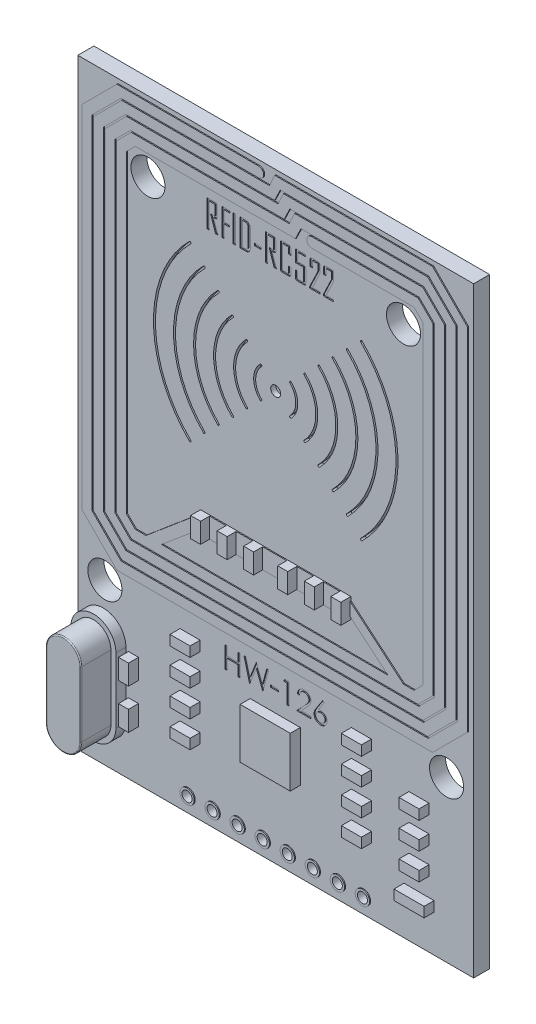
SolidWorks part; units mm, degrees
ref_plane "Alzado" through (0, 0, 0) normal (0, 0, 1) x (1, 0, 0)
ref_plane "Planta" through (0, 0, 0) normal (0, 1, 0) x (1, 0, 0)
ref_plane "Vista lateral" through (0, 0, 0) normal (1, 0, 0) x (0, 0, -1)
sketch "Croquis1" plane through (0, 0, 0) normal (0, 0, 1) x (1, 0, 0)
  line L0 (0, 0) -> (0, 18.9964) construction
  line L1 (-19.75, 30) -> (19.75, 30)
  line L2 (-19.75, 30) -> (-19.75, -30)
  line L3 (-19.75, -30) -> (19.75, -30)
  line L4 (19.75, 30) -> (19.75, -30)
  line L5 (-19.75, 30) -> (19.75, -30) construction
  line L6 (-19.75, -30) -> (19.75, 30) construction
  circle A0 centre (-12.75, 23) radius 1.7
  circle A1 centre (12.75, 23) radius 1.7
  circle A2 centre (-17.05, -14) radius 1.7
  circle A3 centre (17.05, -14) radius 1.7
  point P0 (0, 0)
  dimension "D3" = 3.4
  dimension "D6" = 3.4
  dimension "D1" = 60
  dimension "D2" = 39.5
  dimension "D4" = 7
  dimension "D5" = 7
  dimension "D7" = 2.7
  dimension "D8" = 16
extrude "Saliente-Extruir1" add sketch "Croquis1" along normal blind 1.6
sketch "Croquis2" plane through (0, 0, 1.6) normal (0, 0, 1) x (1, 0, 0)
  line L0 (-17.2, -25.25) -> (-17.2, -18.75) construction
  line L1 (-19.45, -25.25) -> (-19.45, -18.75)
  line L2 (-14.95, -25.25) -> (-14.95, -18.75)
  line L3 (-19.75, 30) -> (-19.75, -30) construction
  line L4 (-19.75, -30) -> (19.75, -30) construction
  arc A0 (-19.45, -25.25) -> (-14.95, -25.25) centre (-17.2, -25.25) ccw
  arc A1 (-14.95, -18.75) -> (-19.45, -18.75) centre (-17.2, -18.75) ccw
  point P2 (-17.2, -22)
  point P9 (-17.2, -27.5)
  dimension "D1" = 2.25
  dimension "D2" = 6.5
  dimension "D3" = 0.3
  dimension "D4" = 2.5
extrude "Saliente-Extruir2" add sketch "Croquis2" along normal blind 1
sketch "Croquis3" plane through (0, 0, 2.6) normal (0, 0, 1) x (1, 0, 0)
  line L0 (-18.95, -18.75) -> (-18.95, -25.25)
  line L1 (-15.45, -25.25) -> (-15.45, -18.75)
  line L2 (-14.95, -25.25) -> (-14.95, -18.75)
  line L3 (-19.45, -18.75) -> (-19.45, -25.25)
  line L4 (-14.95, -25.25) -> (-14.95, -18.75)
  line L5 (-19.45, -18.75) -> (-19.45, -25.25)
  arc A0 (-15.45, -18.75) -> (-18.95, -18.75) centre (-17.2, -18.75) ccw
  arc A1 (-18.95, -25.25) -> (-15.45, -25.25) centre (-17.2, -25.25) ccw
  arc A2 (-19.45, -25.25) -> (-14.95, -25.25) centre (-17.2, -25.25) ccw
  arc A3 (-14.95, -18.75) -> (-19.45, -18.75) centre (-17.2, -18.75) ccw
  arc A4 (-19.45, -25.25) -> (-14.95, -25.25) centre (-17.2, -25.25) ccw
  arc A5 (-14.95, -18.75) -> (-19.45, -18.75) centre (-17.2, -18.75) ccw
  dimension "D1" = 0
  dimension "D2" = 0.5
extrude "Saliente-Extruir3" add sketch "Croquis3" along normal blind 3 contours A0 L0 A1 L1
fillet "Redondeo1" radius 0.1 4 edges at (-17.2, -17, 5.6) (-15.45, -22, 5.6) (-17.2, -27, 5.6) (-18.95, -22, 5.6)
sketch "Croquis4" plane through (0, 0, 1.6) normal (0, 0, 1) x (1, 0, 0)
  line L0 (-19.75, -30) -> (19.75, -30) construction
  line L1 (0, -9.1522) -> (0, -4.1522) construction
  line L2 (-19.25, 26.0478) -> (-15.75, 29.5478)
  line L3 (-18.25, 25.6336) -> (-15.3358, 28.5478)
  line L4 (-19.25, -8.9522) -> (-15.75, -12.4522)
  line L5 (-15.75, 29.5478) -> (-1.601, 29.5478)
  line L6 (-19.25, 26.0478) -> (-19.25, -8.9522)
  line L7 (-15.75, -12.4522) -> (15.75, -12.4522)
  line L8 (19.25, 26.0478) -> (19.25, -8.9522)
  line L9 (15.75, -12.4522) -> (19.25, -8.9522)
  line L10 (15.75, 29.5478) -> (19.25, 26.0478)
  line L11 (-15.3358, 28.5478) -> (-1.601, 28.5478)
  line L12 (15.3358, 28.5478) -> (18.25, 25.6336)
  line L13 (18.25, 25.6336) -> (18.25, -8.538)
  line L14 (15.3358, -11.4522) -> (18.25, -8.538)
  line L15 (-15.3358, -11.4522) -> (15.3358, -11.4522)
  line L16 (-18.25, -8.538) -> (-15.3358, -11.4522)
  line L17 (-18.25, 25.6336) -> (-18.25, -8.538)
  line L19 (-18.1, 25.5714) -> (-15.2737, 28.3978)
  line L20 (-15.2737, 28.3978) -> (-0.5349, 28.3978)
  line L21 (15.2737, 28.3978) -> (18.1, 25.5714)
  line L22 (18.1, 25.5714) -> (18.1, -8.4759)
  line L23 (15.2737, -11.3022) -> (18.1, -8.4759)
  line L24 (-15.2737, -11.3022) -> (15.2737, -11.3022)
  line L25 (-18.1, -8.4759) -> (-15.2737, -11.3022)
  line L26 (-18.1, 25.5714) -> (-18.1, -8.4759)
  line L27 (-17.1, 25.1572) -> (-14.8594, 27.3978)
  line L28 (-14.8594, 27.3978) -> (0, 27.3978)
  line L29 (14.8594, 27.3978) -> (17.1, 25.1572)
  line L30 (17.1, 25.1572) -> (17.1, -8.0617)
  line L31 (14.8594, -10.3022) -> (17.1, -8.0617)
  line L32 (-14.8594, -10.3022) -> (14.8594, -10.3022)
  line L33 (-17.1, -8.0617) -> (-14.8594, -10.3022)
  line L34 (-17.1, 25.1572) -> (-17.1, -8.0617)
  line L36 (-16.95, 25.0951) -> (-14.7973, 27.2478)
  line L37 (-14.7973, 27.2478) -> (0.3296, 27.2478)
  line L38 (14.7973, 27.2478) -> (16.95, 25.0951)
  line L39 (16.95, 25.0951) -> (16.95, -7.9995)
  line L40 (14.7973, -10.1522) -> (16.95, -7.9995)
  line L41 (-14.7973, -10.1522) -> (14.7973, -10.1522)
  line L42 (-16.95, -7.9995) -> (-14.7973, -10.1522)
  line L43 (-16.95, 25.0951) -> (-16.95, -7.9995)
  line L44 (-15.95, 24.6809) -> (-14.3831, 26.2478)
  line L45 (-14.3831, 26.2478) -> (0.9585, 26.2478)
  line L46 (14.3831, 26.2478) -> (15.95, 24.6809)
  line L47 (15.95, 24.6809) -> (15.95, -7.5853)
  line L48 (14.3831, -9.1522) -> (15.95, -7.5853)
  line L49 (-14.3831, -9.1522) -> (14.3831, -9.1522)
  line L50 (-15.95, -7.5853) -> (-14.3831, -9.1522)
  line L51 (-15.95, 24.6809) -> (-15.95, -7.5853)
  line L53 (-15.8, 24.6187) -> (-14.321, 26.0978)
  line L54 (-14.321, 26.0978) -> (1.4391, 26.0978)
  line L55 (14.321, 26.0978) -> (15.8, 24.6187)
  line L56 (15.8, 24.6187) -> (15.8, -7.5232)
  line L57 (14.321, -9.0022) -> (15.8, -7.5232)
  line L58 (-14.321, -9.0022) -> (14.321, -9.0022)
  line L59 (-15.8, -7.5232) -> (-14.321, -9.0022)
  line L60 (-15.8, 24.6187) -> (-15.8, -7.5232)
  line L61 (-14.8, 24.2045) -> (-13.9067, 25.0978)
  line L62 (-13.9067, 25.0978) -> (2.0668, 25.0978)
  line L63 (13.9067, 25.0978) -> (14.8, 24.2045)
  line L64 (14.8, 24.2045) -> (14.8, -7.109)
  line L65 (13.9067, -8.0022) -> (14.8, -7.109)
  line L66 (-13.9067, -8.0022) -> (-12.8445, -8.0022)
  line L67 (-14.8, -7.109) -> (-13.9067, -8.0022)
  line L68 (-14.8, 24.2045) -> (-14.8, -7.109)
  line L69 (0.3296, 27.2478) -> (0.8823, 28.3978)
  line L70 (0, 27.3978) -> (0.5526, 28.5478)
  line L71 (0, 29.5478) -> (-0.5349, 28.3978)
  line L72 (0.5526, 28.5478) -> (15.3358, 28.5478)
  line L73 (-15.3358, 28.5478) -> (15.3358, 28.5478) construction
  line L74 (0.8823, 28.3978) -> (15.2737, 28.3978)
  line L75 (-15.2737, 28.3978) -> (15.2737, 28.3978) construction
  line L76 (1.4391, 26.0978) -> (1.9943, 27.2478)
  line L77 (0, 29.5478) -> (15.75, 29.5478)
  line L78 (-15.75, 29.5478) -> (15.75, 29.5478) construction
  line L79 (0.9585, 26.2478) -> (1.5112, 27.3978)
  line L81 (1.9943, 27.2478) -> (14.7973, 27.2478)
  line L82 (-14.7973, 27.2478) -> (14.7973, 27.2478) construction
  line L83 (1.5112, 27.3978) -> (14.8594, 27.3978)
  line L84 (-14.8594, 27.3978) -> (14.8594, 27.3978) construction
  line L85 (2.6219, 26.2478) -> (2.0668, 25.0978)
  line L86 (3.6973, 26.0978) -> (14.321, 26.0978)
  line L87 (-14.321, 26.0978) -> (14.321, 26.0978) construction
  line L88 (2.6219, 26.2478) -> (14.3831, 26.2478)
  line L89 (-14.3831, 26.2478) -> (14.3831, 26.2478) construction
  line L90 (3.6973, 25.0978) -> (13.9067, 25.0978)
  line L91 (-13.9067, 25.0978) -> (13.9067, 25.0978) construction
  line L97 (-7.5, -4.8061) -> (-7.5, -5.1522)
  line L98 (-7.5, -3.1522) -> (7.5, -3.1522)
  line L99 (-7.5, -3.1522) -> (-7.5, -3.4984)
  line L100 (-7.5, -5.1522) -> (7.5, -5.1522)
  line L101 (7.5, -3.1522) -> (7.5, -3.4984)
  line L102 (-7.5, -3.1522) -> (7.5, -5.1522) construction
  line L103 (-7.5, -5.1522) -> (7.5, -3.1522) construction
  line L108 (-7.8222, -3.7699) -> (-12.3908, -7.6199)
  line L109 (-7.5, -4.8061) -> (-11.2927, -8.0022)
  line L112 (19.25, -29.5) -> (19.25, 29.5)
  line L113 (19.25, 29.5) -> (-19.25, 29.5)
  line L114 (-19.25, 29.5) -> (-19.25, -29.5)
  line L115 (-19.25, -29.5) -> (19.25, -29.5)
  line L119 (-19.25, -29.5) -> (19.25, -29.5)
  line L120 (-12.3908, -7.6199) -> (-12.8445, -8.0022)
  line L121 (-7.8222, -3.7699) -> (-7.5, -3.4984)
  line L122 (-11.2927, -8.0022) -> (11.2927, -8.0022)
  line L123 (-13.9067, -8.0022) -> (13.9067, -8.0022) construction
  line L124 (7.5, -4.8061) -> (11.2927, -8.0022)
  line L125 (7.8222, -3.7699) -> (7.5, -3.4984)
  line L126 (12.3908, -7.6199) -> (12.8445, -8.0022)
  line L127 (7.8222, -3.7699) -> (12.3908, -7.6199)
  line L128 (7.5, -4.8061) -> (7.5, -5.1522)
  line L129 (12.8445, -8.0022) -> (13.9067, -8.0022)
  arc A0 (-1.601, 28.5478) -> (-1.601, 29.5478) centre (-1.601, 29.0478) ccw
  arc A1 (3.6973, 26.0978) -> (3.6973, 25.0978) centre (3.6973, 25.5978) ccw
  point P6 (-19.25, 29.5478)
  point P7 (19.25, -12.4522)
  point P9 (-19.25, -12.4522)
  point P10 (19.25, 29.5478)
  dimension "D2" = 1
  dimension "D3" = 42
  dimension "D4" = 38.5
  dimension "D7" = 1
  dimension "D11" = 1
  dimension "D5" = 5
  dimension "D6" = 15
  dimension "D12" = 17.5478
  dimension "D13" = 2
  dimension "D14" = 0.5
extrude "Saliente-Extruir4" add sketch "Croquis4" along normal blind 0.1 contours L86 A1 L90 L63 L64 L65 L129 L126 L127 L125 L101 L98 L99 L121 L108 L120 L66 L67 L68 L61 L62 L85 L88 L46 L47 L48 L49 L50 L51 L44 L45 L79 L83 L29 L30 L31 L32 L33 L34 L27 L28 L70 L72 L12 L13 L14 L15 L16 L17 L3 L11
sketch "Croquis5" plane through (0, 0, 1.6) normal (0, 0, 1) x (1, 0, 0)
  line L1 (0, -3.1522) -> (0, 6.8478) construction
  line L2 (-7.5, -3.1522) -> (7.5, -3.1522) construction
  line L3 (-0.5, 10.8478) -> (-9.5579, 10.8478) construction
  circle A1 centre (0, 10.8478) radius 0.5
  arc A2 (-1.4142, 12.262) -> (-1.4142, 9.4336) centre (0, 10.8478) ccw
  arc A3 (-1.5556, 12.4034) -> (-1.5556, 9.2921) centre (0, 10.8478) ccw
  arc A4 (-2.8284, 13.6762) -> (-2.8284, 8.0194) centre (0, 10.8478) ccw
  arc A5 (-2.9698, 13.8176) -> (-2.9698, 7.8779) centre (0, 10.8478) ccw
  arc A6 (-4.2426, 15.0904) -> (-4.2426, 6.6051) centre (0, 10.8478) ccw
  arc A7 (-4.3841, 15.2318) -> (-4.3841, 6.4637) centre (0, 10.8478) ccw
  arc A8 (-5.6569, 16.5046) -> (-5.6569, 5.1909) centre (0, 10.8478) ccw
  arc A9 (-5.7983, 16.6461) -> (-5.7983, 5.0495) centre (0, 10.8478) ccw
  arc A10 (-7.0711, 17.9188) -> (-7.0711, 3.7767) centre (0, 10.8478) ccw
  arc A11 (-7.2125, 18.0603) -> (-7.2125, 3.6353) centre (0, 10.8478) ccw
  arc A12 (-8.4853, 19.3331) -> (-8.4853, 2.3625) centre (0, 10.8478) ccw
  arc A13 (-8.6267, 19.4745) -> (-8.6267, 2.2211) centre (0, 10.8478) ccw
  circle A14 centre (0, 10.8478) radius 12.2 construction
  circle A15 centre (0, 10.8478) radius 12 construction
  circle A16 centre (0, 10.8478) radius 10.2 construction
  circle A17 centre (0, 10.8478) radius 10 construction
  circle A18 centre (0, 10.8478) radius 8.2 construction
  circle A19 centre (0, 10.8478) radius 8 construction
  circle A20 centre (0, 10.8478) radius 6.2 construction
  circle A21 centre (0, 10.8478) radius 6 construction
  circle A22 centre (0, 10.8478) radius 4.2 construction
  circle A23 centre (0, 10.8478) radius 4 construction
  circle A24 centre (0, 10.8478) radius 2.2 construction
  circle A25 centre (0, 10.8478) radius 2 construction
  arc A26 (-8.4853, 2.3625) -> (-8.6267, 2.2211) centre (-8.556, 2.2918) cw
  arc A27 (-7.2125, 3.6353) -> (-7.0711, 3.7767) centre (-7.1418, 3.706) ccw
  arc A28 (-5.7983, 5.0495) -> (-5.6569, 5.1909) centre (-5.7276, 5.1202) ccw
  arc A29 (-4.3841, 6.4637) -> (-4.2426, 6.6051) centre (-4.3134, 6.5344) ccw
  arc A30 (-2.9698, 7.8779) -> (-2.8284, 8.0194) centre (-2.8991, 7.9486) ccw
  arc A31 (-1.5556, 9.2921) -> (-1.4142, 9.4336) centre (-1.4849, 9.3629) ccw
  arc A32 (-8.6267, 19.4745) -> (-8.4853, 19.3331) centre (-8.556, 19.4038) cw
  arc A33 (-7.0711, 17.9188) -> (-7.2125, 18.0603) centre (-7.1418, 17.9896) ccw
  arc A34 (-5.6569, 16.5046) -> (-5.7983, 16.6461) centre (-5.7276, 16.5753) ccw
  arc A35 (-1.4142, 12.262) -> (-1.5556, 12.4034) centre (-1.4849, 12.3327) ccw
  arc A36 (-4.2426, 15.0904) -> (-4.3841, 15.2318) centre (-4.3134, 15.1611) ccw
  arc A37 (-2.8284, 13.6762) -> (-2.9698, 13.8176) centre (-2.8991, 13.7469) ccw
  arc A38 (2.8284, 13.6762) -> (2.9698, 13.8176) centre (2.8991, 13.7469) cw
  arc A39 (4.2426, 15.0904) -> (4.3841, 15.2318) centre (4.3134, 15.1611) cw
  arc A40 (1.4142, 12.262) -> (1.5556, 12.4034) centre (1.4849, 12.3327) cw
  arc A41 (5.6569, 16.5046) -> (5.7983, 16.6461) centre (5.7276, 16.5753) cw
  arc A42 (7.0711, 17.9188) -> (7.2125, 18.0603) centre (7.1418, 17.9896) cw
  arc A43 (8.6267, 19.4745) -> (8.4853, 19.3331) centre (8.556, 19.4038) ccw
  arc A44 (1.5556, 9.2921) -> (1.4142, 9.4336) centre (1.4849, 9.3629) cw
  arc A45 (2.9698, 7.8779) -> (2.8284, 8.0194) centre (2.8991, 7.9486) cw
  arc A46 (4.3841, 6.4637) -> (4.2426, 6.6051) centre (4.3134, 6.5344) cw
  arc A47 (5.7983, 5.0495) -> (5.6569, 5.1909) centre (5.7276, 5.1202) cw
  arc A48 (7.2125, 3.6353) -> (7.0711, 3.7767) centre (7.1418, 3.706) cw
  arc A49 (8.4853, 2.3625) -> (8.6267, 2.2211) centre (8.556, 2.2918) ccw
  arc A50 (8.6267, 19.4745) -> (8.6267, 2.2211) centre (0, 10.8478) cw
  arc A51 (8.4853, 19.3331) -> (8.4853, 2.3625) centre (0, 10.8478) cw
  arc A52 (7.2125, 18.0603) -> (7.2125, 3.6353) centre (0, 10.8478) cw
  arc A53 (7.0711, 17.9188) -> (7.0711, 3.7767) centre (0, 10.8478) cw
  arc A54 (5.7983, 16.6461) -> (5.7983, 5.0495) centre (0, 10.8478) cw
  arc A55 (5.6569, 16.5046) -> (5.6569, 5.1909) centre (0, 10.8478) cw
  arc A56 (4.3841, 15.2318) -> (4.3841, 6.4637) centre (0, 10.8478) cw
  arc A57 (4.2426, 15.0904) -> (4.2426, 6.6051) centre (0, 10.8478) cw
  arc A58 (2.9698, 13.8176) -> (2.9698, 7.8779) centre (0, 10.8478) cw
  arc A59 (2.8284, 13.6762) -> (2.8284, 8.0194) centre (0, 10.8478) cw
  arc A60 (1.5556, 12.4034) -> (1.5556, 9.2921) centre (0, 10.8478) cw
  arc A61 (1.4142, 12.262) -> (1.4142, 9.4336) centre (0, 10.8478) cw
  dimension "D1" = 0.2
  dimension "D2" = 2
  dimension "D3" = 2
  dimension "D4" = 2
  dimension "D5" = 2
  dimension "D6" = 2
extrude "Cortar-Extruir1" cut sketch "Croquis5" against normal blind 0.5
sketch "Croquis7" plane through (0, 0, 1.6) normal (0, 0, 1) x (1, 0, 0)
  line L0 (-7.5, -5.1522) -> (7.5, -5.1522) construction
  line L1 (-7.5, -3.1522) -> (-6.5, -3.1522)
  line L2 (-7.5, -3.1522) -> (-7.5, -5.1522)
  line L3 (-7.5, -5.1522) -> (-6.5, -5.1522)
  line L4 (-6.5, -3.1522) -> (-6.5, -5.1522)
  line L5 (0, -5.1522) -> (0, -7.1403) construction
  line L6 (-7.5, -5.1522) -> (7.5, -5.1522) construction
  line L7 (7.5, -5.1522) -> (6.5, -5.1522)
  line L8 (7.5, -3.1522) -> (6.5, -3.1522)
  line L9 (-4.85, -3.1522) -> (-4.85, -5.1522)
  line L10 (-4.85, -3.1522) -> (-3.85, -3.1522)
  line L11 (-3.85, -3.1522) -> (-3.85, -5.1522)
  line L12 (-4.85, -5.1522) -> (-3.85, -5.1522)
  line L13 (2.2, -5.1522) -> (1.2, -5.1522)
  line L14 (-2.2, -3.1522) -> (-2.2, -5.1522)
  line L15 (-2.2, -3.1522) -> (-1.2, -3.1522)
  line L16 (-1.2, -3.1522) -> (-1.2, -5.1522)
  line L17 (-2.2, -5.1522) -> (-1.2, -5.1522)
  line L18 (-7.5, -3.1522) -> (-6.5, -3.1522)
  line L19 (-7.5, -5.1522) -> (-6.5, -5.1522)
  line L20 (1.2, -3.1522) -> (1.2, -5.1522)
  line L21 (2.2, -3.1522) -> (1.2, -3.1522)
  line L22 (2.2, -3.1522) -> (2.2, -5.1522)
  line L23 (4.85, -5.1522) -> (3.85, -5.1522)
  line L24 (3.85, -3.1522) -> (3.85, -5.1522)
  line L25 (4.85, -3.1522) -> (3.85, -3.1522)
  line L26 (4.85, -3.1522) -> (4.85, -5.1522)
  line L27 (6.5, -3.1522) -> (6.5, -5.1522)
  line L28 (7.5, -5.1522) -> (6.5, -5.1522)
  line L29 (7.5, -3.1522) -> (7.5, -5.1522)
  line L30 (7.5, -3.1522) -> (6.5, -3.1522)
  dimension "D1" = 1
  dimension "D2" = 3
extrude "Saliente-Extruir5" add sketch "Croquis7" along normal blind 1 contours L4 L1 L2 L3 | L9 L12 L11 L10 | L14 L17 L16 L15 | L22 L21 L20 L13 | L26 L25 L24 L23 | L29 L8 L27 L7
sketch "Croquis8" plane through (0, 0, 1.6) normal (0, 0, 1) x (1, 0, 0)
  line L0 (0, -30) -> (0, -25.4316) construction
  line L1 (-2.5511, -17) -> (2.4489, -17)
  line L2 (-2.5511, -17) -> (-2.5511, -22)
  line L3 (-2.5511, -22) -> (2.4489, -22)
  line L4 (2.4489, -17) -> (2.4489, -22)
  line L5 (-2.5511, -17) -> (2.4489, -22) construction
  line L6 (-2.5511, -22) -> (2.4489, -17) construction
  line L7 (-9.5511, -14.4522) -> (-7.5511, -14.4522)
  line L8 (-9.5511, -14.4522) -> (-9.5511, -15.4522)
  line L9 (-9.5511, -15.4522) -> (-7.5511, -15.4522)
  line L10 (-7.5511, -14.4522) -> (-7.5511, -15.4522)
  line L11 (-9.5511, -14.4522) -> (-7.5511, -15.4522) construction
  line L12 (-9.5511, -15.4522) -> (-7.5511, -14.4522) construction
  line L13 (-19.75, -30) -> (19.75, -30) construction
  line L14 (19.75, 30) -> (-19.75, 30) construction
  line L15 (19.75, -30) -> (19.75, 30) construction
  line L16 (-15.75, -12.4522) -> (15.75, -12.4522) construction
  line L17 (-9.5511, -17.1122) -> (-9.5511, -18.1122)
  line L18 (-9.5511, -17.1122) -> (-7.5511, -17.1122)
  line L19 (-7.5511, -17.1122) -> (-7.5511, -18.1122)
  line L20 (-9.5511, -18.1122) -> (-7.5511, -18.1122)
  line L21 (-9.5511, -19.7722) -> (-9.5511, -20.7722)
  line L22 (-9.5511, -19.7722) -> (-7.5511, -19.7722)
  line L23 (-7.5511, -19.7722) -> (-7.5511, -20.7722)
  line L24 (-9.5511, -20.7722) -> (-7.5511, -20.7722)
  line L25 (-9.5511, -22.4322) -> (-9.5511, -23.4322)
  line L26 (-9.5511, -22.4322) -> (-7.5511, -22.4322)
  line L27 (-7.5511, -22.4322) -> (-7.5511, -23.4322)
  line L28 (-9.5511, -23.4322) -> (-7.5511, -23.4322)
  line L29 (9.5511, -15.4522) -> (7.5511, -14.4522) construction
  line L30 (9.5511, -14.4522) -> (7.5511, -15.4522) construction
  line L31 (9.5511, -23.4322) -> (7.5511, -23.4322)
  line L32 (7.5511, -22.4322) -> (7.5511, -23.4322)
  line L33 (9.5511, -22.4322) -> (7.5511, -22.4322)
  line L34 (9.5511, -22.4322) -> (9.5511, -23.4322)
  line L35 (9.5511, -20.7722) -> (7.5511, -20.7722)
  line L36 (7.5511, -19.7722) -> (7.5511, -20.7722)
  line L37 (9.5511, -19.7722) -> (7.5511, -19.7722)
  line L38 (9.5511, -19.7722) -> (9.5511, -20.7722)
  line L39 (9.5511, -18.1122) -> (7.5511, -18.1122)
  line L40 (7.5511, -17.1122) -> (7.5511, -18.1122)
  line L41 (9.5511, -17.1122) -> (7.5511, -17.1122)
  line L42 (9.5511, -17.1122) -> (9.5511, -18.1122)
  line L43 (7.5511, -14.4522) -> (7.5511, -15.4522)
  line L44 (9.5511, -15.4522) -> (7.5511, -15.4522)
  line L45 (9.5511, -14.4522) -> (9.5511, -15.4522)
  line L46 (9.5511, -14.4522) -> (7.5511, -14.4522)
  line L47 (-14.6935, -23.004) -> (-14.6935, -25.004)
  line L48 (-14.6935, -19.004) -> (-13.6935, -19.004)
  line L49 (-14.6935, -19.004) -> (-14.6935, -21.004)
  line L50 (-14.6935, -21.004) -> (-13.6935, -21.004)
  line L51 (-13.6935, -19.004) -> (-13.6935, -21.004)
  line L52 (-14.6935, -19.004) -> (-13.6935, -21.004) construction
  line L53 (-14.6935, -21.004) -> (-13.6935, -19.004) construction
  line L54 (-14.6935, -23.004) -> (-13.6935, -23.004)
  line L55 (-13.6935, -23.004) -> (-13.6935, -25.004)
  line L56 (-14.6935, -25.004) -> (-13.6935, -25.004)
  line L57 (15.3011, -19.7722) -> (13.3011, -19.7722)
  line L58 (15.3011, -17.1122) -> (13.3011, -17.1122)
  line L59 (13.3011, -19.7722) -> (13.3011, -20.7722)
  line L60 (15.3011, -18.1122) -> (13.3011, -18.1122)
  line L61 (13.3011, -17.1122) -> (13.3011, -18.1122)
  line L62 (13.3011, -22.4322) -> (13.3011, -23.4322)
  line L63 (15.3011, -20.7722) -> (13.3011, -20.7722)
  line L64 (15.3011, -19.7722) -> (15.3011, -20.7722)
  line L65 (15.3011, -22.4322) -> (13.3011, -22.4322)
  line L66 (15.3011, -23.4322) -> (13.3011, -23.4322)
  line L67 (15.3011, -22.4322) -> (15.3011, -23.4322)
  line L68 (15.3011, -17.1122) -> (15.3011, -18.1122)
  line L69 (14.3011, -23.4322) -> (14.3011, -25.7821) construction
  line L71 (12.8011, -25.2821) -> (15.8011, -25.2821)
  line L72 (12.8011, -25.2821) -> (12.8011, -26.2821)
  line L73 (12.8011, -26.2821) -> (15.8011, -26.2821)
  line L74 (15.8011, -25.2821) -> (15.8011, -26.2821)
  line L75 (12.8011, -25.2821) -> (15.8011, -26.2821) construction
  line L76 (12.8011, -26.2821) -> (15.8011, -25.2821) construction
  point P0 (-0.0511, -19.5)
  point P5 (-8.5511, -14.9522)
  point P49 (8.5511, -14.9522)
  point P50 (-14.1935, -20.004)
  dimension "D1" = 2
  dimension "D2" = 1
  dimension "D3" = 5
  dimension "D4" = 5
  dimension "D5" = 52
  dimension "D6" = 17.3011
  dimension "D7" = 12
  dimension "D8" = 2
  dimension "D10" = 1
  dimension "D11" = 2
  dimension "D13" = 4.4489
  dimension "D14" = 1
  dimension "D15" = 4.4489
  dimension "D16" = 6.5678
  dimension "D17" = 3
  dimension "D18" = 2
  dimension "D19" = 2
  dimension "D9" = 4
  dimension "D12" = 2
extrude "Saliente-Extruir6" add sketch "Croquis8" along normal blind 1
sketch "Croquis9" plane through (0, 0, 1.6) normal (0, 0, 1) x (1, 0, 0)
  line L0 (0, -30) -> (0, -28.5) construction
  line L1 (-19.75, -30) -> (19.75, -30) construction
  line L2 (-10, -28.5) -> (-8.75, -28.5) construction
  line L3 (-10, -29.75) -> (10, -29.75)
  line L4 (-10, -29.75) -> (-10, -27.25)
  line L5 (-10, -27.25) -> (10, -27.25)
  line L6 (10, -29.75) -> (10, -27.25)
  line L7 (-10, -29.75) -> (10, -27.25) construction
  line L8 (-10, -27.25) -> (10, -29.75) construction
  line L9 (19.75, -30) -> (19.75, 30) construction
  circle A0 centre (-8.75, -28.5) radius 0.5
  circle A1 centre (-6.25, -28.5) radius 0.5
  circle A2 centre (-3.75, -28.5) radius 0.5
  circle A3 centre (-1.25, -28.5) radius 0.5
  circle A4 centre (1.25, -28.5) radius 0.5
  circle A5 centre (3.75, -28.5) radius 0.5
  circle A6 centre (6.25, -28.5) radius 0.5
  circle A7 centre (8.75, -28.5) radius 0.5
  dimension "D5" = 1
  dimension "D1" = 1.5
  dimension "D2" = 20
  dimension "D3" = 2.5
  dimension "D4" = 1.25
  dimension "D6" = 8
extrude "Cortar-Extruir3" cut sketch "Croquis9" against normal through all contours A1 | A2 | A3 | A4 | A5 | A6 | A7 | A0
sketch "Croquis10" plane through (0, 0, 1.6) normal (0, 0, 1) x (1, 0, 0)
  circle A2 centre (-8.75, -28.5) radius 0.5
  circle A3 centre (-8.75, -28.5) radius 0.7175
extrude "Saliente-Extruir7" add sketch "Croquis10" along normal blind 0.1
pattern_linear "MatrizL3" count 8 spacing 2.5 along (1, 0, 0) of "Saliente-Extruir7"
sketch "Croquis11" plane through (0, 0, 1.6) normal (0, 0, 1) x (1, 0, 0)
  text T0 "RFID-RC522" font "Agency FB" height in points 10
extrude "Cortar-Extruir4" cut sketch "Croquis11" against normal blind 0.1
sketch "Croquis12" plane through (0, 0, 1.6) normal (0, 0, 1) x (1, 0, 0)
  text T0 "HW-126" font "Century Gothic" height in points 8
extrude "Cortar-Extruir5" cut sketch "Croquis12" against normal blind 0.1
